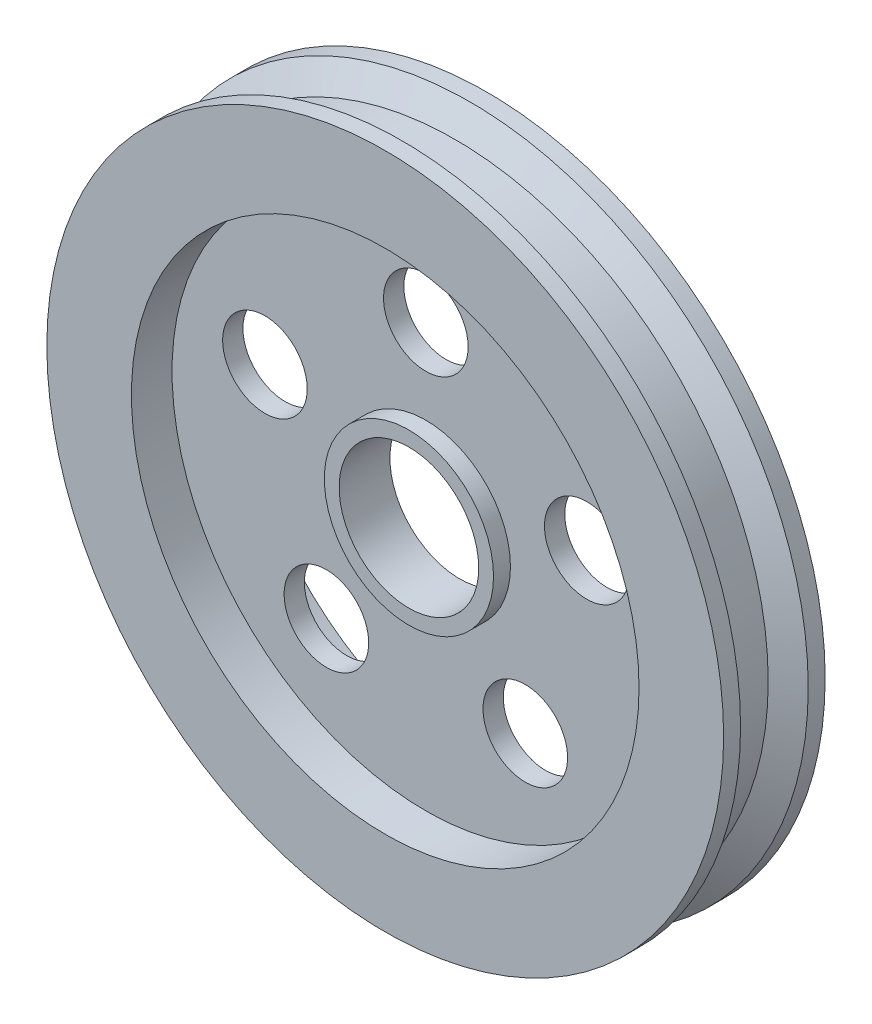
SolidWorks part; units mm, degrees
ref_plane "Front Plane" through (0, 0, 0) normal (0, 0, 1) x (1, 0, 0)
ref_plane "Top Plane" through (0, 0, 0) normal (0, 1, 0) x (1, 0, 0)
ref_plane "Right Plane" through (0, 0, 0) normal (1, 0, 0) x (0, 0, -1)
sketch "Sketch1" plane through (0, 0, 0) normal (0, 0, 1) x (1, 0, 0)
  circle A0 centre (0, 0) radius 4
  circle A1 centre (0, 0) radius 20
  dimension "D1" = 8
  dimension "20" = 40
extrude "Boss-Extrude1" add sketch "Sketch1" along normal mid plane 6
sketch "Sketch3" plane through (0, 0, 3) normal (0, 0, 1) x (1, 0, 0)
  circle A0 centre (0, 0) radius 15
  dimension "D1" = 30
extrude "Cut-Extrude1" cut sketch "Sketch3" against normal blind 2.4 contours A0
mirror "Mirror1" about plane through (0, 0, 0) normal (0, 0, 1) of "Cut-Extrude1"
sketch "Sketch4" plane through (0, 0, 0.6) normal (0, 0, 1) x (1, 0, 0)
  circle A0 centre (0, 10) radius 2.5
  dimension "D1" = 10
  dimension "D2" = 5
extrude "Cut-Extrude2" cut sketch "Sketch4" against normal through all
pattern_circular "CirPattern1" count 5 over 360 about axis through (0, 0, 0) along (0, 0, 1) of "Cut-Extrude2"
sketch "Sketch5" plane through (0, 0, 0) normal (0, 1, 0) x (1, 0, 0)
  line L0 (0, 0) -> (0, 6.988) construction
  line L1 (20, 2) -> (18.5, 1.134)
  line L2 (20, -3) -> (20, 3) construction
  line L3 (18.5, 1.134) -> (18.5, -1.134)
  line L4 (18.5, -1.134) -> (20, -2)
  line L5 (20, 2) -> (20, -2)
  dimension "D1" = 1.5
  dimension "D2" = 1
  dimension "D3" = 1
  dimension "D4" = 60
  dimension "D5" = 60
revolve "Cut-Revolve1" cut sketch "Sketch5" angle 360 about L0
sketch "Sketch14" plane through (0, 0, 0.6) normal (0, 0, 1) x (1, 0, 0)
  circle A0 centre (0, 0) radius 5
  dimension "D1" = 10
extrude "Boss-Extrude3" add sketch "Sketch14" along normal blind 1 and the other way blind 2 contours A0
sketch "Sketch16" plane through (0, 0, 1.6) normal (0, 0, 1) x (1, 0, 0)
  circle A0 centre (0, 0) radius 4.125
  dimension "D1" = 8.25
extrude "Cut-Extrude3" cut sketch "Sketch16" against normal through all
